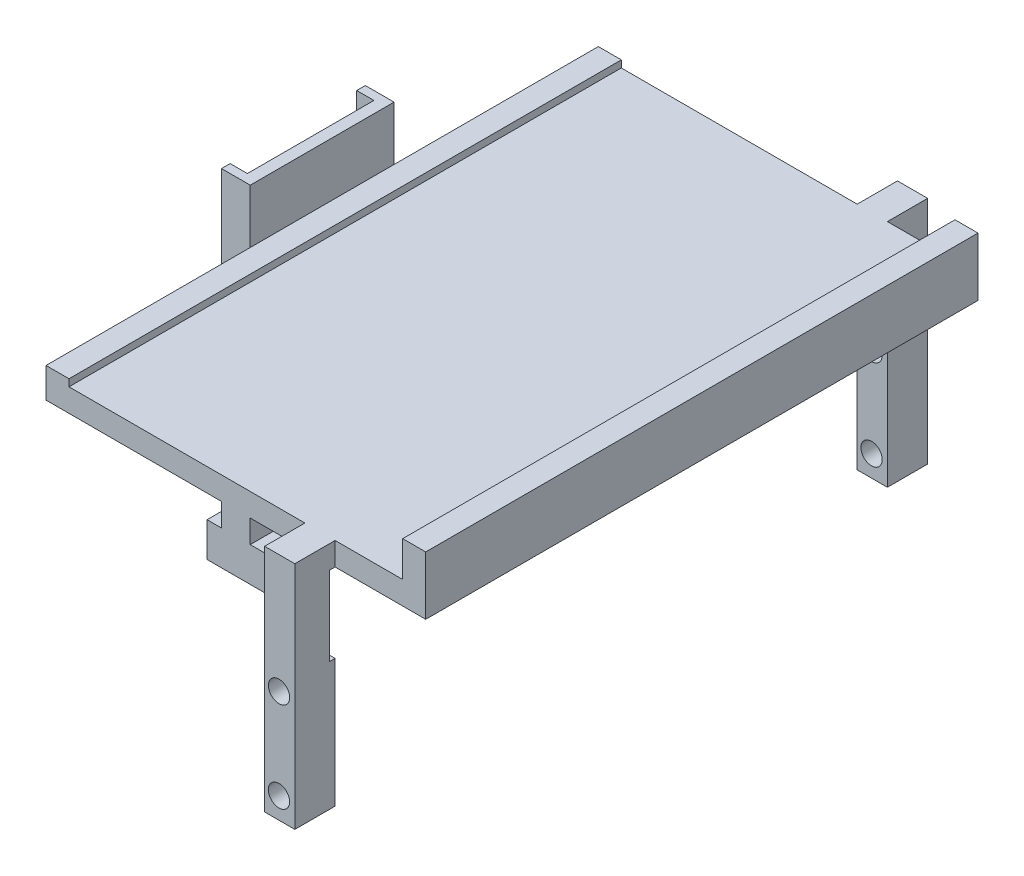
SolidWorks part; units mm, degrees
material "ABS"
ref_plane "Front Plane" through (0, 0, 0) normal (0, 0, 1) x (1, 0, 0)
ref_plane "Top Plane" through (0, 0, 0) normal (0, 1, 0) x (1, 0, 0)
ref_plane "Right Plane" through (0, 0, 0) normal (1, 0, 0) x (0, 0, -1)
sketch "Sketch1" plane through (0, 0, 0) normal (0, 0, 1) x (1, 0, 0)
  line L0 (2.5, 3) -> (5, 3)
  line L1 (-5, 3) -> (-2.5, 3)
  line L2 (-5, 3) -> (-5, -3)
  line L3 (-5, -3) -> (5, -3)
  line L4 (5, 3) -> (5, -3)
  line L5 (-5, 3) -> (5, -3) construction
  line L6 (-5, -3) -> (5, 3) construction
  line L8 (-2.5, 3) -> (-2.5, 7)
  line L10 (2.5, 3) -> (2.5, 7)
  line L11 (-2.5, 7) -> (-33, 7)
  line L12 (-33, 7) -> (-33, 15.7204)
  line L13 (-33, 15.7204) -> (-29, 15.7204)
  line L14 (-29, 15.7204) -> (-29, 11)
  line L15 (-29, 11) -> (29, 11)
  line L16 (2.5, 7) -> (33, 7)
  line L17 (33, 7) -> (33, 17.1483)
  line L18 (33, 17.1483) -> (29, 17.1483)
  line L19 (29, 17.1483) -> (29, 11)
  point P0 (0, 0)
  dimension "D1" = 6
  dimension "D2" = 10
  dimension "D3" = 4
  dimension "D4" = 2.5
  dimension "D5" = 5
  dimension "D6" = 24
  dimension "D7" = 58
  dimension "D8" = 4
  dimension "D9" = 4
  dimension "D10" = 4
extrude "Boss-Extrude1" add sketch "Sketch1" against normal blind 96
sketch "Sketch3" plane through (-5, 0, 0) normal (-1, 0, 0) x (0, 0, 1)
  line L0 (-96, -3) -> (0, -3) construction
  line L1 (-82, -3) -> (-14, -3)
  line L2 (-82, -3) -> (-82, 7)
  line L3 (-82, 7) -> (-14, 7)
  line L4 (-14, -3) -> (-14, 7)
  line L5 (-96, 7) -> (0, 7) construction
  line L6 (-96, 3) -> (-96, -3) construction
  line L7 (0, 3) -> (0, -3) construction
  dimension "D1" = 14
  dimension "D2" = 14
extrude "Cut-Extrude1" cut sketch "Sketch3" against normal blind 96
sketch "Sketch4" plane through (0, 11, 0) normal (0, 1, 0) x (1, 0, 0)
sketch "Sketch6" plane through (0, 0, 0) normal (0, 0, 1) x (1, 0, 0)
  line L1 (2.5, 7) -> (33, 7) construction
  line L3 (12, 7) -> (17.25, 7)
  line L4 (12, 7) -> (12, -29)
  line L5 (12, -29) -> (17.25, -29)
  line L6 (17.25, 7) -> (17.25, -29)
  line L7 (5, -3) -> (5, 3) construction
  line L8 (29, 11) -> (-29, 11) construction
  dimension "D1" = 40
  dimension "D2" = 5.25
  dimension "D3" = 7
extrude "Boss-Extrude3" add sketch "Sketch6" against normal blind 103 and the other way blind 7
sketch "Sketch8" plane through (0, 7, 0) normal (0, 1, 0) x (1, 0, 0)
  line L1 (12, 103) -> (17.25, 103)
  line L2 (12, 103) -> (12, 96)
  line L3 (12, 96) -> (17.25, 96)
  line L4 (17.25, 103) -> (17.25, 96)
extrude "Boss-Extrude4" add sketch "Sketch8" along normal up to surface (4 mm away) up to face at (0, 11, -48)
sketch "Sketch10" plane through (0, 7, 0) normal (0, 1, 0) x (1, 0, 0)
  line L1 (12, 0) -> (17.25, 0)
  line L2 (12, 0) -> (12, -7)
  line L3 (12, -7) -> (17.25, -7)
  line L4 (17.25, 0) -> (17.25, -7)
extrude "Boss-Extrude5" add sketch "Sketch10" along normal up to surface (4 mm away) up to face at (7.3125, 11, -73.75)
sketch "Sketch11" plane through (12, 0, 0) normal (-1, 0, 0) x (0, 0, 1)
  line L0 (7, -29) -> (-103, -29) construction
  line L1 (-96, 7) -> (0, 7)
  line L2 (-96, 7) -> (-96, -29)
  line L3 (-96, -29) -> (0, -29)
  line L4 (0, 7) -> (0, -29)
extrude "Cut-Extrude2" cut sketch "Sketch11" against normal blind 101
sketch "Sketch12" plane through (0, 0, 7) normal (0, 0, 1) x (1, 0, 0)
  line L3 (12, -29) -> (17.25, -29) construction
  line L4 (12, 11) -> (12, -29) construction
  circle A0 centre (14.5, -25.3) radius 1.85
  circle A1 centre (14.5, -9.6) radius 1.85
  dimension "D1" = 3.7
  dimension "D4" = 3.7
  dimension "D2" = 3.7
  dimension "D3" = 15.7
  dimension "D5" = 2.5
extrude "Cut-Extrude3" cut sketch "Sketch12" against normal through all
sketch "Sketch13" plane through (-33, 0, 0) normal (-1, 0, 0) x (0, 0, 1)
  line L0 (0, 15.7204) -> (0, 7) construction
  line L1 (-96, 15.7204) -> (0, 15.7204)
  line L2 (-96, 15.7204) -> (-96, 12.2204)
  line L3 (-96, 12.2204) -> (0, 12.2204)
  line L4 (0, 15.7204) -> (0, 12.2204)
  dimension "D1" = 3.5
extrude "Cut-Extrude4" cut sketch "Sketch13" against normal blind 10
sketch "Sketch14" plane through (12, 0, 0) normal (-1, 0, 0) x (0, 0, 1)
  line L1 (0, 7) -> (1, 7)
  line L2 (0, 7) -> (0, -6.7532)
  line L3 (0, -6.7532) -> (1, -6.7532)
  line L4 (1, 7) -> (1, -6.7532)
  line L5 (-96, 7) -> (-97, 7)
  line L6 (-96, 7) -> (-96, -6.7532)
  line L7 (-96, -6.7532) -> (-97, -6.7532)
  line L8 (-97, 7) -> (-97, -6.7532)
  dimension "D1" = 13.7532
  dimension "D2" = 1
extrude "Cut-Extrude5" cut sketch "Sketch14" against normal blind 10
sketch "Sketch15" plane through (-33, 0, 0) normal (-1, 0, 0) x (0, 0, 1)
  line L0 (-96, 12.2204) -> (-96, 7) construction
  line L1 (-60.5, 21.6102) -> (-35.5, 21.6102)
  line L2 (-60.5, 21.6102) -> (-60.5, -2.3898)
  line L3 (-60.5, -2.3898) -> (-35.5, -2.3898)
  line L4 (-35.5, 21.6102) -> (-35.5, -2.3898)
  line L5 (-60.5, 21.6102) -> (-35.5, -2.3898) construction
  line L6 (-60.5, -2.3898) -> (-35.5, 21.6102) construction
  line L7 (-96, 7) -> (0, 7) construction
  point P0 (-48, 9.6102)
  point P8 (-96, 9.6102)
  point P11 (-48, 7)
  dimension "D1" = 25
  dimension "D2" = 24
extrude "Boss-Extrude6" add sketch "Sketch15" along normal blind 5
sketch "Sketch16" plane through (-38, 0, 0) normal (-1, 0, 0) x (0, 0, 1)
  line L1 (-59, 21.6102) -> (-37, 21.6102)
  line L2 (-59, 21.6102) -> (-59, -2.3898)
  line L3 (-59, -2.3898) -> (-37, -2.3898)
  line L4 (-37, 21.6102) -> (-37, -2.3898)
  line L5 (-59, 21.6102) -> (-37, -2.3898) construction
  line L6 (-59, -2.3898) -> (-37, 21.6102) construction
  line L8 (-60.5, 21.6102) -> (-60.5, -2.3898) construction
  line L10 (-60.5, -2.3898) -> (-35.5, -2.3898) construction
  point P0 (-48, 9.6102)
  dimension "D1" = 22
  dimension "D2" = 24
  dimension "D4" = 1.5
extrude "Cut-Extrude6" cut sketch "Sketch16" against normal blind 3
